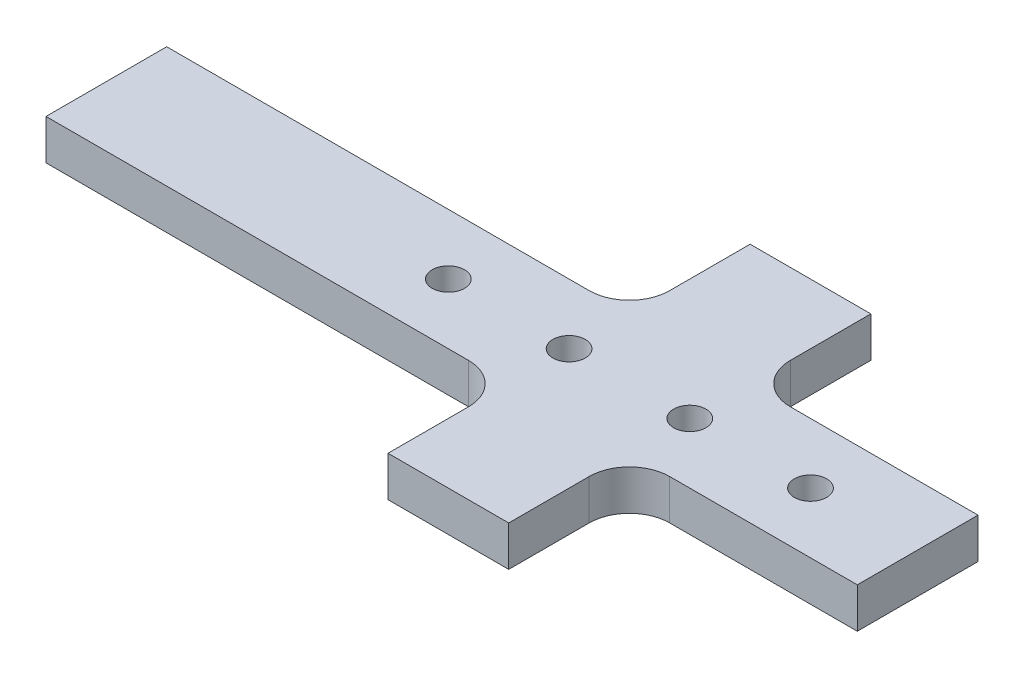
SolidWorks part; units mm, degrees
material "AISI 304"
ref_plane "Front Plane" through (0, 0, 0) normal (0, 0, 1) x (1, 0, 0)
ref_plane "Top Plane" through (0, 0, 0) normal (0, 1, 0) x (1, 0, 0)
ref_plane "Right Plane" through (0, 0, 0) normal (1, 0, 0) x (0, 0, -1)
sketch "Sketch1" plane through (0, 0, 0) normal (0, 1, 0) x (1, 0, 0)
  line L0 (-74.827, -9.525) -> (-15.875, -9.525) construction
  line L5 (-9.525, -15.875) -> (-9.525, -28.575) construction
  line L6 (-9.525, -28.575) -> (9.525, -28.575) construction
  line L7 (9.525, -28.575) -> (9.525, -15.875) construction
  line L8 (15.875, -9.525) -> (45.4855, -9.525) construction
  line L9 (45.4855, -9.525) -> (45.4855, 9.525) construction
  line L10 (45.4855, 9.525) -> (15.875, 9.525) construction
  line L11 (9.525, 15.875) -> (9.525, 28.575) construction
  line L12 (9.525, 28.575) -> (-9.525, 28.575) construction
  line L13 (-9.525, 28.575) -> (-9.525, 15.875) construction
  line L14 (-15.875, 9.525) -> (-75.0596, 9.525) construction
  line L15 (-74.827, -9.525) -> (-15.875, -9.525)
  line L16 (-9.525, -15.875) -> (-9.525, -28.575)
  line L17 (-9.525, -28.575) -> (9.525, -28.575)
  line L18 (9.525, -28.575) -> (9.525, -15.875)
  line L19 (15.875, -9.525) -> (45.4855, -9.525)
  line L20 (45.4855, -9.525) -> (45.4855, 9.525)
  line L21 (45.4855, 9.525) -> (15.875, 9.525)
  line L22 (9.525, 15.875) -> (9.525, 28.575)
  line L23 (9.525, 28.575) -> (-9.525, 28.575)
  line L24 (-9.525, 28.575) -> (-9.525, 15.875)
  line L25 (-15.875, 9.525) -> (-75.0596, 9.525)
  line L26 (-74.827, -9.525) -> (-82.55, -9.525)
  line L27 (-82.55, -9.525) -> (-82.55, 9.525)
  line L28 (-82.55, 9.525) -> (-75.0596, 9.525)
  arc A0 (-9.525, -15.875) -> (-15.875, -9.525) centre (-15.875, -15.875) ccw construction
  arc A1 (15.875, -9.525) -> (9.525, -15.875) centre (15.875, -15.875) ccw construction
  arc A2 (9.525, 15.875) -> (15.875, 9.525) centre (15.875, 15.875) ccw construction
  arc A3 (-15.875, 9.525) -> (-9.525, 15.875) centre (-15.875, 15.875) ccw construction
  arc A4 (-9.525, -15.875) -> (-15.875, -9.525) centre (-15.875, -15.875) ccw
  arc A5 (15.875, -9.525) -> (9.525, -15.875) centre (15.875, -15.875) ccw
  arc A6 (9.525, 15.875) -> (15.875, 9.525) centre (15.875, 15.875) ccw
  arc A7 (-15.875, 9.525) -> (-9.525, 15.875) centre (-15.875, 15.875) ccw
  dimension "D1" = 6.35
extrude "Boss-Extrude1" add sketch "Sketch1" along normal blind 6.35
hole_wizard "1/4-20 Tapped Hole1" positions "Sketch4" profile "Sketch5" tap size "1/4-20" standard "ANSI Inch" end condition through all
sketch "Sketch4" plane through (0, 0, 0) normal (0, -1, 0) x (-1, 0, 0)
  point P0 (28.575, 0)
  point P4 (28.575, 0)
  dimension "D1" = 28.575
cosmetic thread "Hole Thread1" parameters "D2"=6.35
sketch "Sketch5" plane through (-28.575, 0, 0) normal (1, 0, 0) x (0, 0, -1)
  line L0 (0, 0) -> (0, 6.35)
  line L1 (0, 6.35) -> (2.5527, 6.35)
  line L2 (2.5527, 6.35) -> (2.5527, 0)
  line L5 (2.5527, 0) -> (0, 0)
  line L11 (0, -6.35) -> (0, 107.95) construction
  dimension "Thru Tap Drill Dia." = 5.1054
  dimension "Thru Tap Drill Depth" = 6.35
cosmetic thread "Hole Thread2" parameters "D2"=6.35
pattern_linear "LPattern1" count 4 spacing 19.05 along (1, 0, 0) of "1/4-20 Tapped Hole1"
